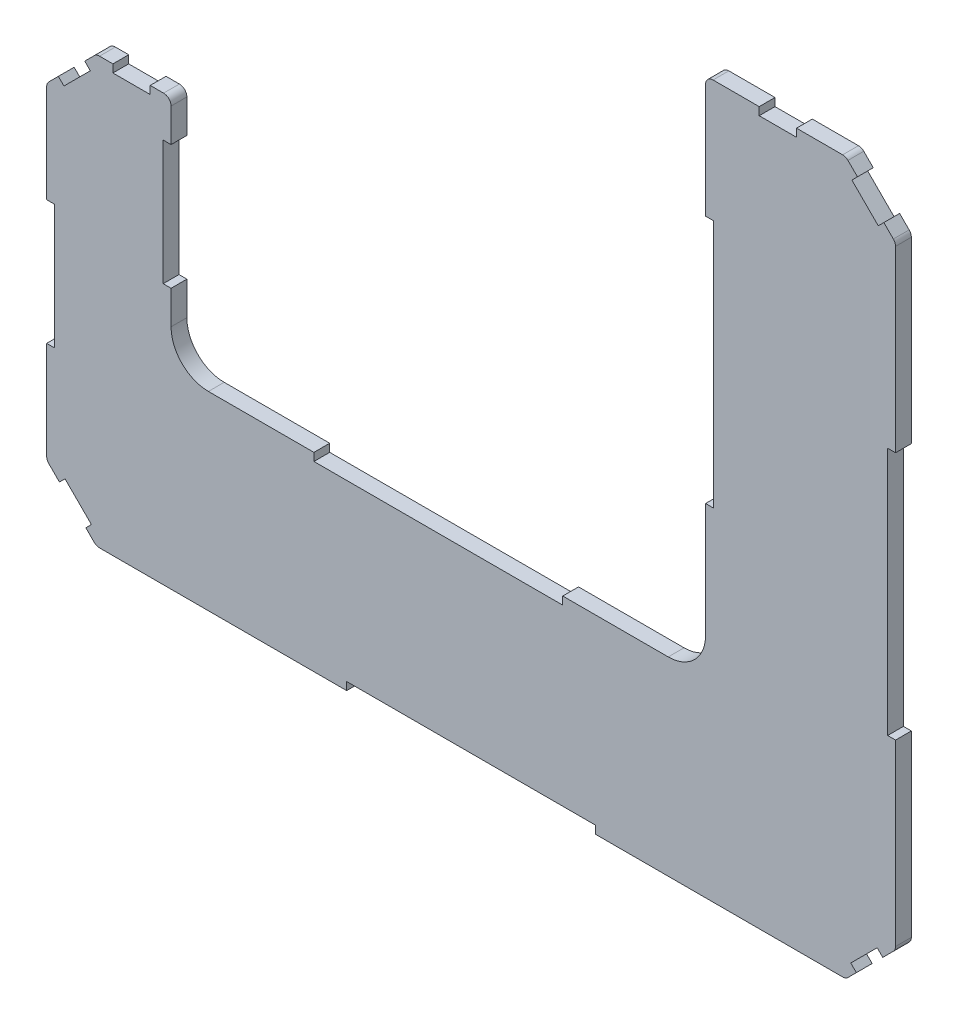
SolidWorks part; units mm, degrees
material "Teak"
ref_plane "Front Plane" through (0, 0, 0) normal (0, 0, 1) x (1, 0, 0)
ref_plane "Top Plane" through (0, 0, 0) normal (0, 1, 0) x (1, 0, 0)
ref_plane "Right Plane" through (0, 0, 0) normal (1, 0, 0) x (0, 0, -1)
sketch "Sketch2" plane through (0, 0, 0) normal (0, 0, 1) x (1, 0, 0)
  line L0 (-157.4125, 94.825) -> (-107.4125, 94.825)
  line L1 (-107.4125, 94.825) -> (-107.4125, 0)
  line L2 (-107.4125, 0) -> (107.4125, 0)
  line L3 (107.4125, 0) -> (107.4125, 209.825)
  line L4 (107.4125, 209.825) -> (183.7625, 209.825)
  line L5 (183.7625, 209.825) -> (183.7625, -76.35)
  line L6 (183.7625, -76.35) -> (58.275, -76.35)
  line L7 (-31.925, -76.35) -> (58.275, -76.35)
  line L10 (-31.925, -76.35) -> (-157.4125, -76.35)
  line L11 (-157.4125, -76.35) -> (-157.4125, 94.825)
  line L12 (-37.4125, 0) -> (-37.4125, 144.825) construction
  point P10 (-37.4125, 0)
  point P14 (107.4125, 144.825)
  point P15 (-37.4125, 94.825)
  dimension "D1" = 144.825
  dimension "D2" = 144.825
  dimension "D6" = 90.2
  dimension "D7" = 76.35
  dimension "D10" = 50
  dimension "D11" = 50
extrude "Boss-Extrude1" add sketch "Sketch2" along normal blind 3.175 and the other way blind 3.175
chamfer "Chamfer1" distance 20 angle 45 4 edges at (-157.4125, -76.35, 0) (183.7625, -76.35, 0) (183.7625, 209.825, 0) (-157.4125, 94.825, 0)
fillet "Fillet1" radius 15 2 edges at (107.4125, 0, 0) (-107.4125, 0, 0)
fillet "Fillet2" radius 3 8 edges at (183.7625, -56.35, 0) (-157.4125, -56.35, 0) (-157.4125, 74.825, 0) (-137.4125, 94.825, 0) (-107.4125, 94.825, 0) (183.7625, 189.825, 0) (163.7625, 209.825, 0) (107.4125, 209.825, 0)
sketch "Sketch3" plane through (0, 0, 3.175) normal (0, 0, 1) x (1, 0, 0)
  line L0 (-94.6381, 69.9757) -> (-94.6381, 14.7992)
  line L1 (-94.6381, 14.7992) -> (-97.8131, 14.7992)
  line L2 (-97.8131, 14.7992) -> (-97.8131, 69.9757)
  line L3 (-97.8131, 69.9757) -> (-94.6381, 69.9757)
  line L4 (-127.4635, 65.4691) -> (-114.3536, 78.579)
  line L5 (-114.3536, 78.579) -> (-112.1085, 76.3339)
  line L6 (-112.1085, 76.3339) -> (-125.2184, 63.2241)
  line L7 (-125.2184, 63.2241) -> (-127.4635, 65.4691)
  line L8 (-129.3392, 54.7846) -> (-126.1642, 54.7846)
  line L9 (-126.1642, 54.7846) -> (-126.1642, -28.3138)
  line L10 (-126.1642, -28.3138) -> (-129.3392, -28.3138)
  line L11 (-129.3392, -28.3138) -> (-129.3392, 54.7846)
  line L12 (-127.4635, -37.1329) -> (-125.2184, -34.8879)
  line L13 (-125.2184, -34.8879) -> (-110.9382, -49.1681)
  line L14 (-110.9382, -49.1681) -> (-113.1832, -51.4132)
  line L15 (-113.1832, -51.4132) -> (-127.4635, -37.1329)
  line L16 (-67.7784, -44.3183) -> (-67.7784, -41.1433)
  line L17 (-67.7784, -41.1433) -> (53.0181, -41.1433)
  line L18 (53.0181, -41.1433) -> (53.0181, -44.3183)
  line L19 (53.0181, -44.3183) -> (-67.7784, -44.3183)
  line L20 (114.9313, -49.5303) -> (117.1763, -51.7753)
  line L21 (117.1763, -51.7753) -> (131.7883, -37.1634)
  line L22 (131.7883, -37.1634) -> (129.5432, -34.9183)
  line L23 (129.5432, -34.9183) -> (114.9313, -49.5303)
  line L24 (-67.7784, -4.1746) -> (-67.7784, -7.3496)
  line L25 (-67.7784, -7.3496) -> (63.5847, -7.3496)
  line L26 (63.5847, -7.3496) -> (63.5847, -4.1746)
  line L27 (63.5847, -4.1746) -> (-67.7784, -4.1746)
  line L28 (92.7516, 20.9162) -> (91.2159, 151.9937)
  line L29 (91.2159, 151.9937) -> (94.3909, 151.9937)
  line L30 (94.3909, 151.9937) -> (95.9266, 20.9162)
  line L31 (95.9266, 20.9162) -> (92.7516, 20.9162)
  line L32 (96.8341, 161.8762) -> (96.8341, 158.7012)
  line L33 (96.8341, 158.7012) -> (112.5649, 158.7012)
  line L34 (112.5649, 158.7012) -> (112.5649, 161.8762)
  line L35 (112.5649, 161.8762) -> (96.8341, 161.8762)
  line L37 (117.7781, 156.4535) -> (120.0231, 158.6985)
  line L38 (120.0231, 158.6985) -> (133.8694, 144.8523)
  line L39 (133.8694, 144.8523) -> (131.6243, 142.6072)
  line L40 (131.6243, 142.6072) -> (117.7781, 156.4535)
  line L41 (129.9213, 134.1701) -> (133.0963, 134.1701)
  line L42 (133.0963, 134.1701) -> (133.0963, -24.961)
  line L43 (133.0963, -24.961) -> (129.9213, -24.961)
  line L44 (129.9213, -24.961) -> (129.9213, 134.1701)
  line L45 (163.7625, -76.35) -> (182.8838, -57.2287) construction
  line L46 (-156.5338, -57.2287) -> (-137.4125, -76.35) construction
  line L47 (-138.2912, 93.9463) -> (-156.5338, 75.7037) construction
  line L48 (182.8838, 190.7037) -> (164.6412, 208.9463) construction
  dimension "D1" = 3.175
extrude "Cut-Extrude1" [suppressed] cut sketch "Sketch3" against normal through all
sketch "magnets" plane through (0, 0, 3.175) normal (0, 0, 1) x (1, 0, 0)
  point P0 (94.6751, 158.4052)
  point P1 (114.7572, -50)
  point P2 (131.9288, 140.6094)
  point P3 (131.9288, -32.8111)
  point P4 (0, -44.1618)
  point P5 (-114.0039, -50)
  point P6 (-130.8821, -32.8111)
  point P9 (-130.8821, 62.3605)
  point P10 (-93.5499, 79.7316)
  point P12 (0, -4.7392)
sketch "Sketch4" plane through (0, 0, 3.175) normal (0, 0, 1) x (1, 0, 0)
  line L0 (128.9662, 209.825) -> (128.9662, 206.65)
  line L1 (162.5199, 209.825) -> (110.4125, 209.825) construction
  line L2 (128.9662, 206.65) -> (143.9662, 206.65)
  line L3 (143.9662, 206.65) -> (143.9662, 209.825)
  line L4 (168.4592, 205.1283) -> (166.2141, 202.8832)
  line L5 (-138.2912, 93.9463) -> (-156.5338, 75.7037) construction
  line L6 (166.2141, 202.8832) -> (176.8207, 192.2766)
  line L7 (176.8207, 192.2766) -> (179.0658, 194.5217)
  line L8 (-107.4125, 15) -> (-107.4125, 91.825) construction
  line L9 (-107.4125, 78.4125) -> (-110.5875, 78.4125)
  line L11 (-107.4125, 78.4125) -> (-107.4125, 28.4125)
  line L12 (-107.4125, 28.4125) -> (-110.5875, 28.4125)
  line L13 (-110.5875, 78.4125) -> (-110.5875, 28.4125)
  line L15 (-157.4125, 73.5824) -> (-157.4125, -55.1074) construction
  line L16 (-157.4125, 34.2375) -> (-154.2375, 34.2375)
  line L17 (-137.4125, -76.35) -> (163.7625, -76.35) construction
  line L19 (-157.4125, 34.2375) -> (-157.4125, -15.7625)
  line L20 (-157.4125, -15.7625) -> (-154.2375, -15.7625)
  line L21 (-154.2375, 34.2375) -> (-154.2375, -15.7625)
  line L23 (-152.2765, -61.486) -> (-141.6699, -72.0926)
  line L24 (-156.5338, -57.2287) -> (-137.4125, -76.35) construction
  line L25 (-141.6699, -72.0926) -> (-139.4248, -69.8476)
  line L26 (-139.4248, -69.8476) -> (-150.0314, -59.241)
  line L27 (-150.0314, -59.241) -> (-152.2765, -61.486)
  line L28 (-152.7158, 79.5217) -> (-150.4707, 77.2766)
  line L29 (-144.7281, -64.5443) -> (-146.9732, -66.7893) construction
  line L30 (-150.4707, 77.2766) -> (-139.8641, 87.8832)
  line L31 (-139.8641, 87.8832) -> (-142.1092, 90.1283)
  line L32 (-130.7912, 94.825) -> (-130.7912, 91.65)
  line L33 (-36.825, -76.35) -> (63.175, -76.35)
  line L35 (-130.7912, 91.65) -> (-115.7912, 91.65)
  line L36 (-36.825, -76.35) -> (-36.825, -73.175)
  line L37 (183.7625, -55.1074) -> (183.7625, 188.5824) construction
  line L39 (-36.825, -73.175) -> (63.175, -73.175)
  line L40 (63.175, -76.35) -> (63.175, -73.175)
  line L41 (-50, -3.175) -> (50, -3.175)
  line L42 (-50, -3.175) -> (-50, 0)
  line L43 (-50, 0) -> (50, 0)
  line L44 (50, -3.175) -> (50, 0)
  line L45 (92.4125, 0) -> (-92.4125, 0) construction
  line L46 (107.4125, 206.825) -> (107.4125, 15) construction
  line L47 (107.4125, 160.9125) -> (110.5875, 160.9125)
  line L48 (107.4125, 160.9125) -> (107.4125, 60.9125)
  line L49 (107.4125, 60.9125) -> (110.5875, 60.9125)
  line L50 (110.5875, 160.9125) -> (110.5875, 60.9125)
  line L51 (182.8838, 190.7037) -> (164.6412, 208.9463) construction
  line L52 (183.7625, 116.7375) -> (180.5875, 116.7375)
  line L53 (183.7625, 116.7375) -> (183.7625, 16.7375)
  line L55 (183.7625, 16.7375) -> (180.5875, 16.7375)
  line L56 (180.5875, 116.7375) -> (180.5875, 16.7375)
  line L57 (168.0199, -72.0926) -> (165.7748, -69.8476)
  line L58 (163.7625, -76.35) -> (182.8838, -57.2287) construction
  line L59 (-147.4125, 84.825) -> (-145.1674, 82.5799) construction
  line L60 (-123.2912, 91.65) -> (-123.2912, 94.825) construction
  line L61 (171.5174, 197.5799) -> (173.7625, 199.825) construction
  line L62 (165.7748, -69.8476) -> (176.3814, -59.241)
  line L63 (176.3814, -59.241) -> (178.6265, -61.486)
  line L64 (171.0781, -64.5443) -> (173.3232, -66.7893)
  line L71 (-115.7912, 91.65) -> (-115.7912, 94.825)
  line L77 (-110.4125, 94.825) -> (-136.1699, 94.825) construction
  point P20 (-110.5875, 53.4125)
  point P21 (-107.4125, 53.4125)
  point P28 (-154.2375, 9.2375)
  point P29 (-157.4125, 9.2375)
  point P36 (-144.7281, -64.5443)
  point P51 (13.175, -76.35)
  point P58 (0, -3.175)
  point P67 (107.4125, 110.9125)
  point P76 (183.7625, 66.7375)
  point P106 (136.4662, 206.65)
  point P107 (136.4662, 209.825)
  point P109 (171.5174, 197.5799)
  line M1 (163.7625, -76.35) -> (182.8838, -57.2287)
  line M3 (183.7625, -55.1074) -> (183.7625, 188.5824)
  line M5 (182.8838, 190.7037) -> (164.6412, 208.9463)
  line M7 (162.5199, 209.825) -> (110.4125, 209.825)
  line M9 (107.4125, 206.825) -> (107.4125, 15)
  line M11 (92.4125, 0) -> (-92.4125, 0)
  line M13 (-107.4125, 15) -> (-107.4125, 91.825)
  line M15 (-110.4125, 94.825) -> (-136.1699, 94.825)
  line M17 (-138.2912, 93.9463) -> (-156.5338, 75.7037)
  line M19 (-157.4125, 73.5824) -> (-157.4125, -55.1074)
  line M21 (-156.5338, -57.2287) -> (-137.4125, -76.35)
  line M28 (-137.4125, -76.35) -> (163.7625, -76.35)
  dimension "D1" = 3.175
  dimension "D2" = 15
  dimension "D3" = 50
  dimension "D4" = 15
  dimension "D5" = 100
extrude "wall_slots" cut sketch "Sketch4" against normal blind 60 contours L9 L13 L12 M13 | L35 L71 L32 M15 | L30 L31 L28 M17 | L21 L16 L20 M19 | L26 L27 L25 M21 | L40 L39 L36 M28 | L41 L44 L42 M11 | L64 L62 L57 M1 | L62 L64 L63 M1 | L52 L56 L55 M3 | L50 L47 L49 M9 | L2 L3 L0 M7 | L6 L7 L4 M5
fillet "Fillet3" radius 3 2 edges at (163.7625, -76.35, 0) (-137.4125, -76.35, 0)
sketch "wall_measure" plane through (0, 0, 3.175) normal (0, 0, 1) x (1, 0, 0)
  line L0 (-136.1699, 94.825) -> (-136.1699, 91.65)
  line L1 (-136.1699, 91.65) -> (-110.4125, 91.65)
  line L2 (-110.4125, 91.65) -> (-110.4125, 94.825)
  line L3 (-110.5875, 78.4125) -> (-110.5875, 28.4125) construction
  line L4 (110.4125, 209.825) -> (110.4125, 206.65)
  line L5 (110.4125, 206.65) -> (162.5199, 206.65)
  line L6 (162.5199, 206.65) -> (162.5199, 209.825)
  line L7 (128.9662, 206.65) -> (143.9662, 206.65) construction
  line L8 (164.6412, 208.9463) -> (162.3961, 206.7013)
  line L9 (162.3961, 206.7013) -> (180.6388, 188.4586)
  line L10 (180.6388, 188.4586) -> (182.8838, 190.7037)
  line L11 (182.8838, 190.7037) -> (179.0658, 194.5217) construction
  line L12 (107.4125, 206.825) -> (110.5875, 206.825)
  line L13 (110.5875, 206.825) -> (110.5875, 15)
  line L14 (110.5875, 15) -> (107.4125, 15)
  line L15 (107.4125, 60.9125) -> (107.4125, 15) construction
  line L16 (183.7625, 188.5824) -> (180.5875, 188.5824)
  line L17 (180.5875, 188.5824) -> (180.5875, -55.1074)
  line L18 (180.5875, -55.1074) -> (183.7625, -55.1074)
  line L19 (-92.4125, 0) -> (-92.4125, -3.175)
  line L20 (-92.4125, -3.175) -> (92.4125, -3.175)
  line L21 (92.4125, -3.175) -> (92.4125, 0)
  line L22 (-36.825, -73.175) -> (63.175, -73.175) construction
  line L23 (162.5199, -76.35) -> (-136.1699, -76.35)
  line L24 (162.5199, -76.35) -> (162.5199, -73.175)
  line L25 (162.5199, -73.175) -> (-136.1699, -73.175)
  line L26 (-136.1699, -76.35) -> (-136.1699, -73.175)
  line L27 (182.8838, -57.2287) -> (180.6388, -54.9836)
  line L28 (180.6388, -54.9836) -> (162.3961, -73.2263)
  line L29 (162.3961, -73.2263) -> (164.6412, -75.4713)
  line L32 (-50, -3.175) -> (50, -3.175) construction
  line L33 (180.5875, 116.7375) -> (180.5875, 16.7375) construction
  line L34 (-157.4125, 73.5824) -> (-154.4125, 73.5824)
  line L35 (-154.4125, 73.5824) -> (-154.4125, -55.1074)
  line L36 (-154.4125, -55.1074) -> (-157.4125, -55.1074)
  line L37 (-107.4125, 91.825) -> (-110.5875, 91.825)
  line L38 (-110.5875, 91.825) -> (-110.5875, 15)
  line L39 (-110.5875, 15) -> (-107.4125, 15)
  line L44 (166.2141, 202.8832) -> (176.8207, 192.2766) construction
  line L46 (165.7748, -69.8476) -> (176.3814, -59.241) construction
  line L47 (-130.7912, 91.65) -> (-115.7912, 91.65) construction
  line L48 (110.5875, 160.9125) -> (110.5875, 60.9125) construction
  line L49 (-156.5338, -57.2287) -> (-154.2888, -54.9836)
  line L50 (-154.2888, -54.9836) -> (-136.0461, -73.2263)
  line L51 (-136.0461, -73.2263) -> (-138.2912, -75.4713)
  line L52 (-141.6699, -72.0926) -> (-138.2912, -75.4713) construction
  line L53 (-139.4248, -69.8476) -> (-150.0314, -59.241) construction
  arc A0 (92.4125, 0) -> (107.4125, 15) centre (92.4125, 15) ccw construction
  arc A1 (-107.4125, 15) -> (-92.4125, 0) centre (-92.4125, 15) ccw construction
  point P98 (-156.5338, -57.2287)
  point P99 (-138.2912, -75.4713)
  dimension "D1" = 25.7574
  dimension "D2" = 52.1074
  dimension "D3" = 25.799
  dimension "D4" = 191.825
  dimension "D5" = 243.6897
  dimension "D6" = 184.825
  dimension "D7" = 298.6897
  dimension "D8" = 25.799
  dimension "D11" = 128.6897
  dimension "D12" = 76.825
  dimension "D13" = 25.799
sketch "Sketch5" plane through (0, 0, 3.175) normal (0, 0, 1) x (1, 0, 0)
  line L60 (176.8207, 192.2766) -> (166.2141, 202.8832)
  line L61 (176.8207, 192.2766) -> (166.2141, 202.8832)
  line L62 (166.2141, 202.8832) -> (168.4592, 205.1283)
  line L63 (166.2141, 202.8832) -> (168.4592, 205.1283)
  line L64 (143.9662, 209.825) -> (143.9662, 206.65)
  line L65 (143.9662, 209.825) -> (143.9662, 206.65)
  line L66 (143.9662, 206.65) -> (128.9662, 206.65)
  line L67 (143.9662, 206.65) -> (128.9662, 206.65)
  line L68 (128.9662, 206.65) -> (128.9662, 209.825)
  line L69 (128.9662, 206.65) -> (128.9662, 209.825)
  line L70 (128.9662, 209.825) -> (110.4125, 209.825)
  line L71 (128.9662, 209.825) -> (110.4125, 209.825)
  line L72 (-107.4125, 28.4125) -> (-110.5875, 28.4125)
  line L73 (-107.4125, 28.4125) -> (-110.5875, 28.4125)
  line L74 (168.4592, 205.1283) -> (164.6412, 208.9463)
  line L75 (162.5199, 209.825) -> (143.9662, 209.825)
  line L76 (107.4125, 60.9125) -> (107.4125, 15)
  line L77 (107.4125, 60.9125) -> (107.4125, 15)
  line L78 (-157.4125, 34.2375) -> (-154.2375, 34.2375)
  line L79 (-157.4125, 34.2375) -> (-154.2375, 34.2375)
  line L80 (107.4125, 206.825) -> (107.4125, 160.9125)
  line L81 (-50, 0) -> (-92.4125, 0)
  line L82 (-50, 0) -> (-92.4125, 0)
  line L83 (-107.4125, 78.4125) -> (-107.4125, 91.825)
  line L84 (-107.4125, 78.4125) -> (-107.4125, 91.825)
  line L85 (92.4125, 0) -> (50, 0)
  line L86 (-115.7912, 94.825) -> (-115.7912, 91.65)
  line L87 (-115.7912, 94.825) -> (-115.7912, 91.65)
  line L88 (-115.7912, 91.65) -> (-130.7912, 91.65)
  line L89 (-115.7912, 91.65) -> (-130.7912, 91.65)
  line L90 (-107.4125, 15) -> (-107.4125, 28.4125)
  line L91 (-130.7912, 91.65) -> (-130.7912, 94.825)
  line L92 (-130.7912, 91.65) -> (-130.7912, 94.825)
  line L93 (-130.7912, 94.825) -> (-136.1699, 94.825)
  line L94 (-130.7912, 94.825) -> (-136.1699, 94.825)
  line L95 (-110.4125, 94.825) -> (-115.7912, 94.825)
  line L96 (-142.1092, 90.1283) -> (-139.8641, 87.8832)
  line L97 (-142.1092, 90.1283) -> (-139.8641, 87.8832)
  line L98 (-139.8641, 87.8832) -> (-150.4707, 77.2766)
  line L99 (-139.8641, 87.8832) -> (-150.4707, 77.2766)
  line L100 (-138.2912, 93.9463) -> (-142.1092, 90.1283)
  line L101 (-150.4707, 77.2766) -> (-152.7158, 79.5217)
  line L102 (-150.4707, 77.2766) -> (-152.7158, 79.5217)
  line L103 (-152.7158, 79.5217) -> (-156.5338, 75.7037)
  line L104 (-152.7158, 79.5217) -> (-156.5338, 75.7037)
  line L105 (-157.4125, 73.5824) -> (-157.4125, 34.2375)
  line L106 (-36.825, -73.175) -> (63.175, -73.175)
  line L107 (-36.825, -73.175) -> (63.175, -73.175)
  line L108 (-157.4125, -15.7625) -> (-157.4125, -55.1074)
  line L109 (-157.4125, -15.7625) -> (-157.4125, -55.1074)
  line L110 (-156.5338, -57.2287) -> (-152.2765, -61.486)
  line L111 (180.5875, 116.7375) -> (183.7625, 116.7375)
  line L112 (180.5875, 116.7375) -> (183.7625, 116.7375)
  line L113 (63.175, -76.35) -> (162.5199, -76.35)
  line L114 (63.175, -76.35) -> (162.5199, -76.35)
  line L115 (164.6412, -75.4713) -> (168.0199, -72.0926)
  line L116 (107.4125, 160.9125) -> (110.5875, 160.9125)
  line L117 (107.4125, 160.9125) -> (110.5875, 160.9125)
  line L118 (-139.4248, -69.8476) -> (-141.6699, -72.0926)
  line L119 (-139.4248, -69.8476) -> (-141.6699, -72.0926)
  line L120 (183.7625, 16.7375) -> (180.5875, 16.7375)
  line L121 (183.7625, 16.7375) -> (180.5875, 16.7375)
  line L122 (164.6412, -75.4713) -> (168.0199, -72.0926)
  line L123 (-141.6699, -72.0926) -> (-138.2912, -75.4713)
  line L124 (178.6265, -61.486) -> (182.8838, -57.2287)
  line L125 (178.6265, -61.486) -> (182.8838, -57.2287)
  line L126 (-154.2375, -15.7625) -> (-157.4125, -15.7625)
  line L127 (-154.2375, -15.7625) -> (-157.4125, -15.7625)
  line L128 (183.7625, 116.7375) -> (183.7625, 188.5824)
  line L129 (183.7625, 116.7375) -> (183.7625, 188.5824)
  line L130 (182.8838, 190.7037) -> (179.0658, 194.5217)
  line L131 (182.8838, 190.7037) -> (179.0658, 194.5217)
  line L132 (-141.6699, -72.0926) -> (-138.2912, -75.4713)
  line L133 (179.0658, 194.5217) -> (176.8207, 192.2766)
  line L134 (179.0658, 194.5217) -> (176.8207, 192.2766)
  line L135 (110.5875, 160.9125) -> (110.5875, 60.9125)
  line L136 (110.5875, 160.9125) -> (110.5875, 60.9125)
  line L137 (183.7625, -55.1074) -> (183.7625, 16.7375)
  line L138 (110.5875, 60.9125) -> (107.4125, 60.9125)
  line L139 (110.5875, 60.9125) -> (107.4125, 60.9125)
  line L140 (50, 0) -> (50, -3.175)
  line L141 (50, 0) -> (50, -3.175)
  line L142 (50, -3.175) -> (-50, -3.175)
  line L143 (50, -3.175) -> (-50, -3.175)
  line L144 (-50, -3.175) -> (-50, 0)
  line L145 (-50, -3.175) -> (-50, 0)
  line L146 (168.4592, 205.1283) -> (164.6412, 208.9463)
  line L147 (162.5199, 209.825) -> (143.9662, 209.825)
  line L148 (-110.5875, 28.4125) -> (-110.5875, 78.4125)
  line L149 (-110.5875, 28.4125) -> (-110.5875, 78.4125)
  line L150 (-110.5875, 78.4125) -> (-107.4125, 78.4125)
  line L151 (-110.5875, 78.4125) -> (-107.4125, 78.4125)
  line L152 (107.4125, 206.825) -> (107.4125, 160.9125)
  line L153 (-154.2375, 34.2375) -> (-154.2375, -15.7625)
  line L154 (-154.2375, 34.2375) -> (-154.2375, -15.7625)
  line L155 (-152.2765, -61.486) -> (-150.0314, -59.241)
  line L156 (-152.2765, -61.486) -> (-150.0314, -59.241)
  line L157 (92.4125, 0) -> (50, 0)
  line L158 (-150.0314, -59.241) -> (-139.4248, -69.8476)
  line L159 (-150.0314, -59.241) -> (-139.4248, -69.8476)
  line L160 (-36.825, -76.35) -> (-36.825, -73.175)
  line L161 (-36.825, -76.35) -> (-36.825, -73.175)
  line L162 (-107.4125, 15) -> (-107.4125, 28.4125)
  line L163 (63.175, -73.175) -> (63.175, -76.35)
  line L164 (63.175, -73.175) -> (63.175, -76.35)
  line L165 (168.0199, -72.0926) -> (165.7748, -69.8476)
  line L166 (168.0199, -72.0926) -> (165.7748, -69.8476)
  line L167 (-110.4125, 94.825) -> (-115.7912, 94.825)
  line L168 (165.7748, -69.8476) -> (176.3814, -59.241)
  line L169 (165.7748, -69.8476) -> (176.3814, -59.241)
  line L170 (176.3814, -59.241) -> (178.6265, -61.486)
  line L171 (176.3814, -59.241) -> (178.6265, -61.486)
  line L172 (-138.2912, 93.9463) -> (-142.1092, 90.1283)
  line L173 (180.5875, 16.7375) -> (180.5875, 116.7375)
  line L174 (180.5875, 16.7375) -> (180.5875, 116.7375)
  line L175 (-136.1699, -76.35) -> (-36.825, -76.35)
  line L176 (-136.1699, -76.35) -> (-36.825, -76.35)
  line L177 (-157.4125, 73.5824) -> (-157.4125, 34.2375)
  line L182 (-156.5338, -57.2287) -> (-152.2765, -61.486)
  line L209 (183.7625, -55.1074) -> (183.7625, 16.7375)
  arc A10 (164.6412, 208.9463) -> (162.5199, 209.825) centre (162.5199, 206.825) ccw
  arc A11 (164.6412, 208.9463) -> (162.5199, 209.825) centre (162.5199, 206.825) ccw
  arc A12 (110.4125, 209.825) -> (107.4125, 206.825) centre (110.4125, 206.825) ccw
  arc A13 (110.4125, 209.825) -> (107.4125, 206.825) centre (110.4125, 206.825) ccw
  arc A14 (92.4125, 0) -> (107.4125, 15) centre (92.4125, 15) ccw
  arc A15 (-107.4125, 15) -> (-92.4125, 0) centre (-92.4125, 15) ccw
  arc A16 (-107.4125, 91.825) -> (-110.4125, 94.825) centre (-110.4125, 91.825) ccw
  arc A17 (-107.4125, 91.825) -> (-110.4125, 94.825) centre (-110.4125, 91.825) ccw
  arc A18 (-136.1699, 94.825) -> (-138.2912, 93.9463) centre (-136.1699, 91.825) ccw
  arc A19 (-136.1699, 94.825) -> (-138.2912, 93.9463) centre (-136.1699, 91.825) ccw
  arc A20 (-156.5338, 75.7037) -> (-157.4125, 73.5824) centre (-154.4125, 73.5824) ccw
  arc A21 (-156.5338, 75.7037) -> (-157.4125, 73.5824) centre (-154.4125, 73.5824) ccw
  arc A22 (-157.4125, -55.1074) -> (-156.5338, -57.2287) centre (-154.4125, -55.1074) ccw
  arc A23 (-157.4125, -55.1074) -> (-156.5338, -57.2287) centre (-154.4125, -55.1074) ccw
  arc A24 (182.8838, -57.2287) -> (183.7625, -55.1074) centre (180.7625, -55.1074) ccw
  arc A25 (182.8838, -57.2287) -> (183.7625, -55.1074) centre (180.7625, -55.1074) ccw
  arc A26 (92.4125, 0) -> (107.4125, 15) centre (92.4125, 15) ccw
  arc A27 (-107.4125, 15) -> (-92.4125, 0) centre (-92.4125, 15) ccw
  arc A28 (183.7625, 188.5824) -> (182.8838, 190.7037) centre (180.7625, 188.5824) ccw
  arc A29 (183.7625, 188.5824) -> (182.8838, 190.7037) centre (180.7625, 188.5824) ccw
  arc A32 (162.5199, -76.35) -> (164.6412, -75.4713) centre (162.5199, -73.35) ccw
  arc A33 (162.5199, -76.35) -> (164.6412, -75.4713) centre (162.5199, -73.35) ccw
  arc A34 (-138.2912, -75.4713) -> (-136.1699, -76.35) centre (-136.1699, -73.35) ccw
  arc A35 (-138.2912, -75.4713) -> (-136.1699, -76.35) centre (-136.1699, -73.35) ccw
  dimension "D1" = 0
equation "\"dX\"= 148mm - \"t_wood\" / 2"
equation "\"dY\"= 148mm - \"t_wood\" / 2"
equation "\"hmotor\"= 70mm"
equation "\"D1@Sketch2\"=\"dY\""
equation "\"D2@Sketch2\"=\"dX\""
equation "\"D5@Sketch2\"=\"hmotor\"+\"t_wood\""
equation "\"D6@Sketch2\"=\"hmotor\"+\"d_floor\"+\"t_wood\"*2"
equation "\"t_wood\"= 0.25in"
equation "\"D1@Boss-Extrude1\"=\"t_wood\"/2"
equation "\"D2@Boss-Extrude1\"=\"t_wood\"/2"
equation "\"D1@Sketch3\"=\"t_wood\"/2"
equation "\"d_floor\"= 7.50mm"
equation "\"D7@Sketch2\"=\"hmotor\" + \"t_wood\""
equation "\"D1@Sketch4\"=\"t_wood\" / 2"
